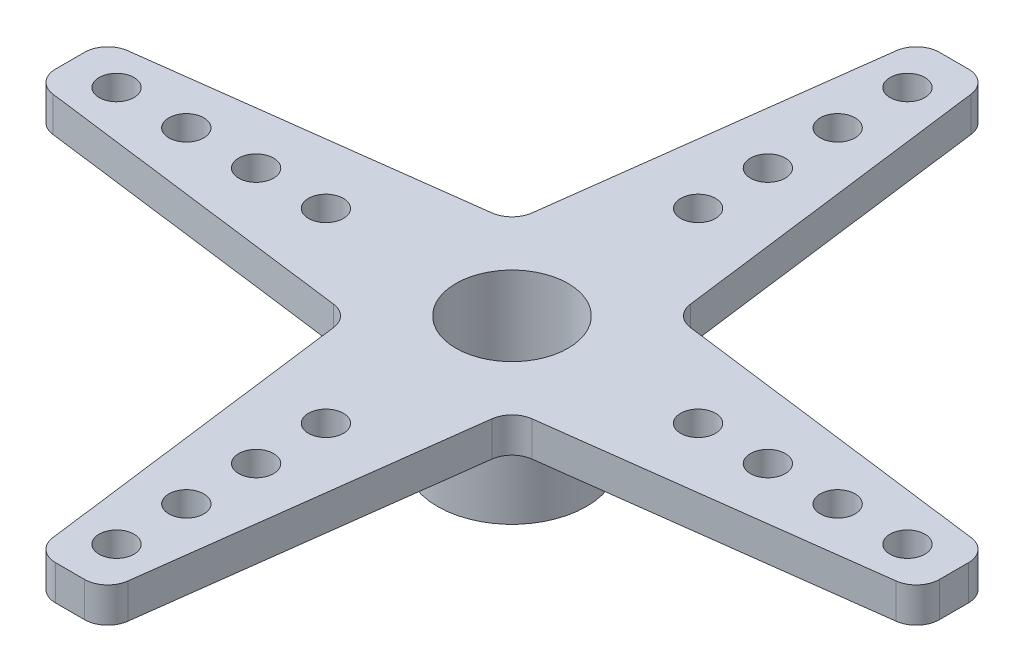
SolidWorks part; units mm, degrees
ref_plane "Front" through (0, 0, 0) normal (0, 0, 1) x (1, 0, 0)
ref_plane "Top" through (0, 0, 0) normal (0, 1, 0) x (1, 0, 0)
ref_plane "Right" through (0, 0, 0) normal (1, 0, 0) x (0, 0, -1)
sketch "Sketch1" plane through (0, 0, 0) normal (0, 1, 0) x (1, 0, 0)
  line L0 (-1.5, 19) -> (-3.5, 3.5)
  line L1 (-3.5, 3.5) -> (-19, 1.5)
  line L2 (-19, 1.5) -> (-19, -1.5)
  line L3 (-19, -1.5) -> (-3.5, -3.5)
  line L4 (-3.5, -3.5) -> (-1.5, -19)
  line L5 (-1.5, -19) -> (1.5, -19)
  line L6 (1.5, -19) -> (3.5, -3.5)
  line L7 (3.5, -3.5) -> (19, -1.5)
  line L8 (19, -1.5) -> (19, 1.5)
  line L9 (19, 1.5) -> (3.5, 3.5)
  line L10 (3.5, 3.5) -> (1.5, 19)
  line L11 (1.5, 19) -> (-1.5, 19)
  circle A0 centre (0, 0) radius 2.413
  circle A1 centre (8, 0) radius 0.75
  circle A2 centre (11, 0) radius 0.75
  circle A3 centre (14, 0) radius 0.75
  circle A4 centre (17, 0) radius 0.75
  circle A5 centre (0, -8) radius 0.75
  circle A6 centre (0, -11) radius 0.75
  circle A7 centre (0, -14) radius 0.75
  circle A8 centre (0, -17) radius 0.75
  circle A9 centre (-8, 0) radius 0.75
  circle A10 centre (-11, 0) radius 0.75
  circle A11 centre (-14, 0) radius 0.75
  circle A12 centre (-17, 0) radius 0.75
  circle A13 centre (0, 8) radius 0.75
  circle A14 centre (0, 11) radius 0.75
  circle A15 centre (0, 14) radius 0.75
  circle A16 centre (0, 17) radius 0.75
  point P38 (0, 0)
  point P49 (0, 19)
  point P50 (-19, 0)
  dimension "D5" = 1.5
  dimension "D6" = 4.826
  dimension "D1" = 8
  dimension "D2" = 11
  dimension "D3" = 14
  dimension "D4" = 17
  dimension "D8" = 19
  dimension "D9" = 3
  dimension "D10" = 7
  dimension "D7" = 4
extrude "Boss-Extrude1" add sketch "Sketch1" along normal blind 1.5
sketch "Sketch2" plane through (0, 0, 0) normal (0, -1, 0) x (1, 0, 0)
  circle A0 centre (0, 0) radius 3.2
  circle A1 centre (0, 0) radius 2.413
  circle A2 centre (0, 0) radius 2.413 construction
  dimension "D1" = 6.4
extrude "Boss-Extrude2" add sketch "Sketch2" along normal blind 4
fillet "Fillet1" radius 1 12 edges at (-3.5, 0.75, -3.5) (-1.5, 0.75, -19) (1.5, 0.75, -19) (3.5, 0.75, -3.5) (19, 0.75, -1.5) (19, 0.75, 1.5) (3.5, 0.75, 3.5) (1.5, 0.75, 19) (-1.5, 0.75, 19) (-3.5, 0.75, 3.5) (-19, 0.75, -1.5) (-19, 0.75, 1.5)
